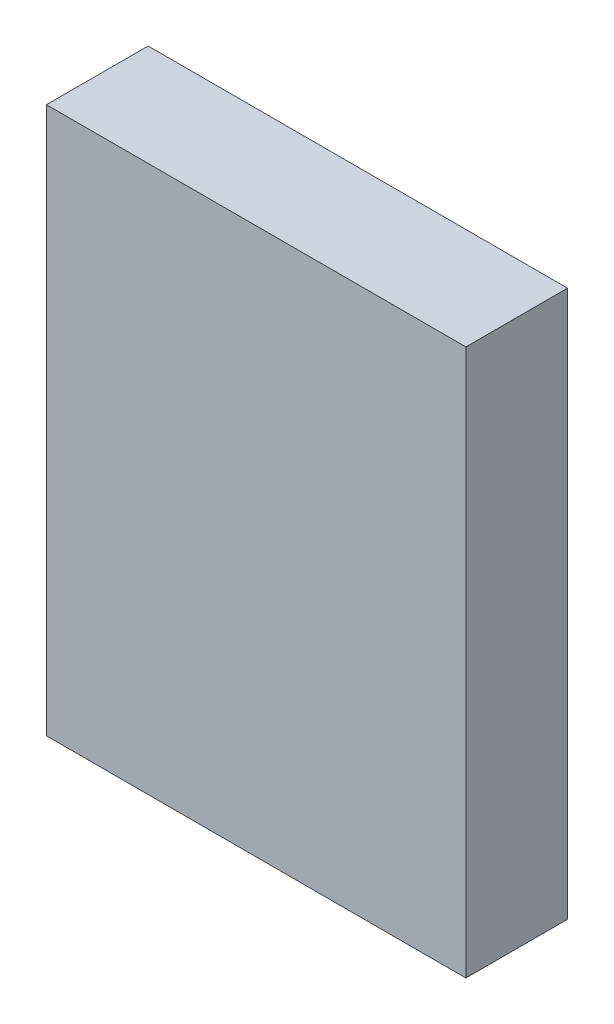
SolidWorks part; units mm, degrees
ref_plane "Front Plane" through (0, 0, 0) normal (0, 0, 1) x (1, 0, 0)
ref_plane "Top Plane" through (0, 0, 0) normal (0, 1, 0) x (1, 0, 0)
ref_plane "Right Plane" through (0, 0, 0) normal (1, 0, 0) x (0, 0, -1)
sketch "Sketch1" plane through (0, 0, 0) normal (0, 0, 1) x (1, 0, 0)
  line L1 (0, 0) -> (52.3875, 0)
  line L2 (0, 0) -> (0, 68.2625)
  line L3 (0, 68.2625) -> (52.3875, 68.2625)
  line L4 (52.3875, 0) -> (52.3875, 68.2625)
  dimension "D1" = 68.2625
  dimension "D2" = 52.3875
extrude "Boss-Extrude1" add sketch "Sketch1" along normal blind 12.7
